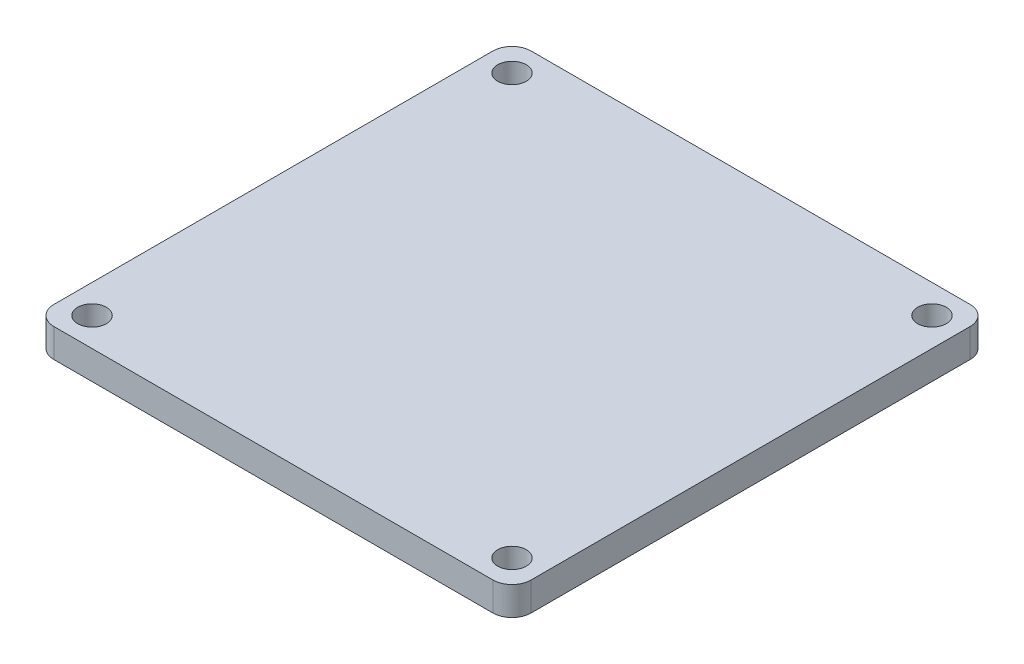
SolidWorks part; units mm, degrees
ref_plane "Front Plane" through (0, 0, 0) normal (0, 0, 1) x (1, 0, 0)
ref_plane "Top Plane" through (0, 0, 0) normal (0, 1, 0) x (1, 0, 0)
ref_plane "Right Plane" through (0, 0, 0) normal (1, 0, 0) x (0, 0, -1)
sketch "Sketch1" plane through (0, 0, 0) normal (0, 1, 0) x (1, 0, 0)
  line L0 (0, 0) -> (0, -25) construction
  line L1 (23, 25) -> (-23, 25)
  line L2 (25, 23) -> (25, -23)
  line L3 (23, -25) -> (-23, -25)
  line L4 (-25, 23) -> (-25, -23)
  line L5 (25, 25) -> (-25, -25) construction
  line L6 (25, -25) -> (-25, 25) construction
  arc A0 (-23, -25) -> (-25, -23) centre (-23, -23) cw
  arc A1 (-23, 25) -> (-25, 23) centre (-23, 23) ccw
  arc A2 (23, 25) -> (25, 23) centre (23, 23) cw
  arc A3 (25, -23) -> (23, -25) centre (23, -23) cw
  circle A4 centre (22, 22) radius 1.5
  circle A5 centre (22, -22) radius 1.5
  circle A6 centre (-22, 22) radius 1.5
  circle A7 centre (-22, -22) radius 1.5
  point P0 (0, 0)
  dimension "D3" = 2
  dimension "D4" = 3
  dimension "D6" = 3
  dimension "D1" = 50
  dimension "D2" = 50
  dimension "D5" = 3
  dimension "D7" = 3
extrude "Boss-Extrude1" add sketch "Sketch1" along normal blind 3
